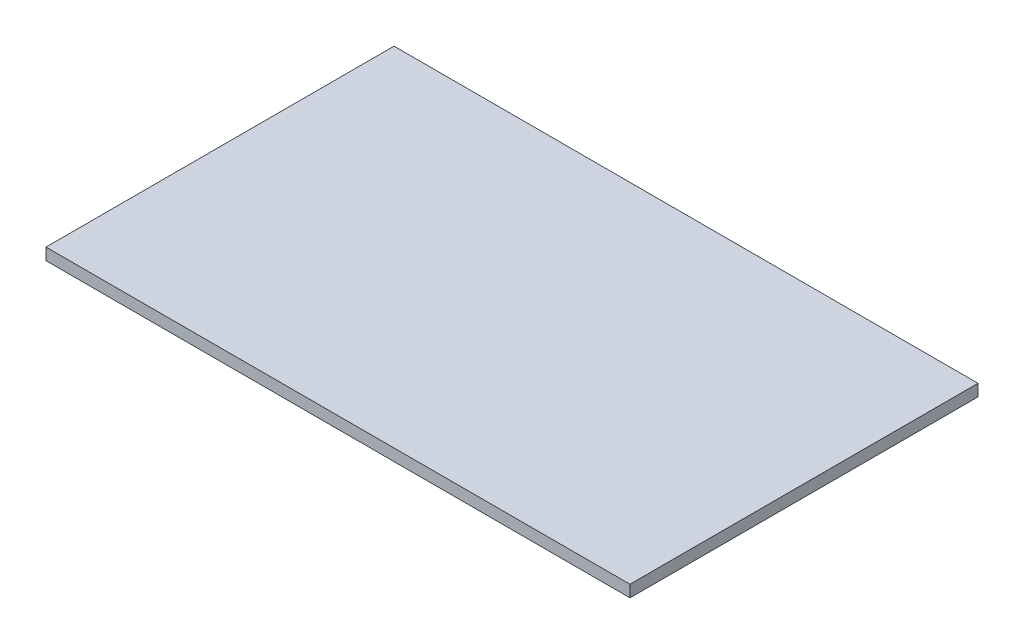
SolidWorks part; units mm, degrees
ref_plane "Front" through (0, 0, 0) normal (0, 0, 1) x (1, 0, 0)
ref_plane "Top" through (0, 0, 0) normal (0, 1, 0) x (1, 0, 0)
ref_plane "Right" through (0, 0, 0) normal (1, 0, 0) x (0, 0, -1)
sketch "Croquis1" plane through (0, 0, 0) normal (0, 1, 0) x (1, 0, 0)
  line L1 (-247.5, 147.5) -> (247.5, 147.5)
  line L2 (-247.5, 147.5) -> (-247.5, -147.5)
  line L3 (-247.5, -147.5) -> (247.5, -147.5)
  line L4 (247.5, 147.5) -> (247.5, -147.5)
  line L5 (-247.5, 147.5) -> (247.5, -147.5) construction
  line L6 (-247.5, -147.5) -> (247.5, 147.5) construction
  point P0 (0, 0)
  dimension "D1" = 495
  dimension "D2" = 295
extrude "Saliente-Extruir1" add sketch "Croquis1" along normal blind 10
